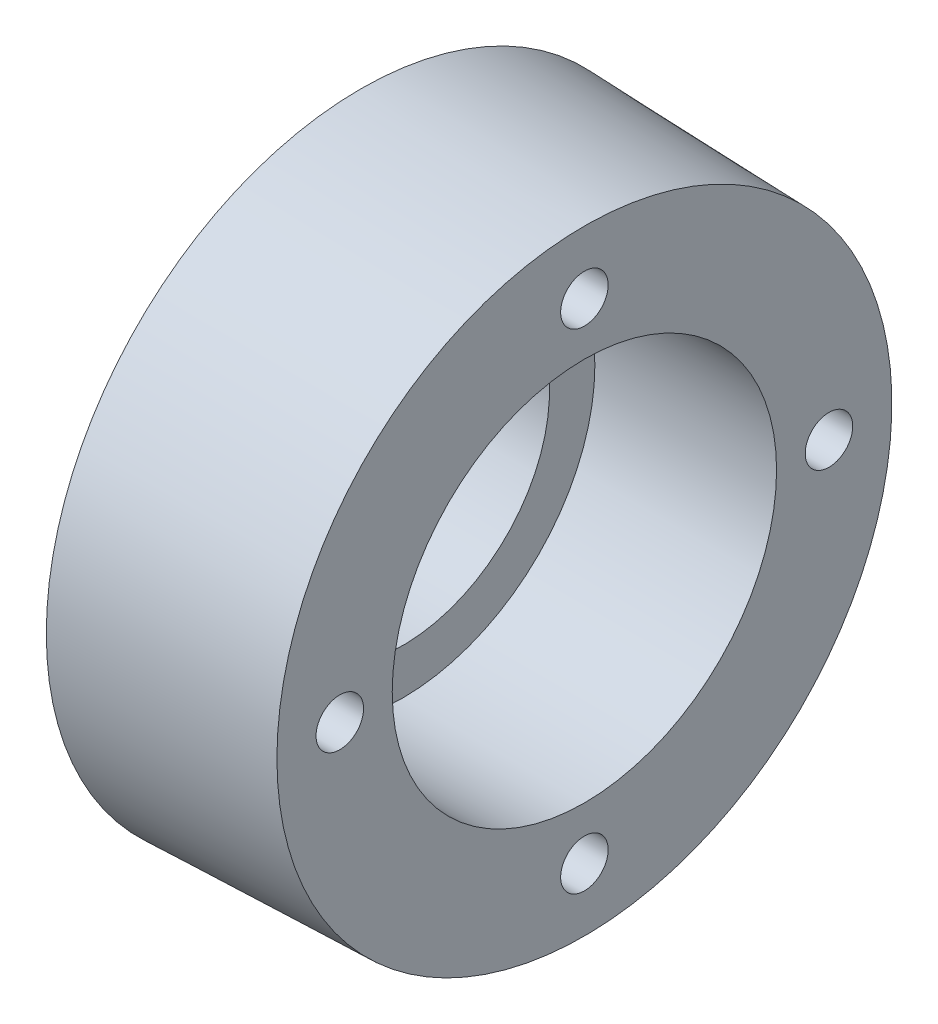
SolidWorks part; units mm, degrees
ref_plane "Front Plane" through (0, 0, 0) normal (0, 0, 1) x (1, 0, 0)
ref_plane "Top Plane" through (0, 0, 0) normal (0, 1, 0) x (1, 0, 0)
ref_plane "Right Plane" through (0, 0, 0) normal (1, 0, 0) x (0, 0, -1)
sketch "Çizim1" plane through (0, 0, 0) normal (0, 0, 1) x (1, 0, 0)
  line L0 (0, 0) -> (76.8972, 0) construction
  line L1 (0, 21) -> (11, 21)
  line L2 (0, 21) -> (0, 28)
  line L3 (0, 28) -> (5, 28)
  line L4 (5, 28) -> (5, 45)
  line L5 (5, 45) -> (37, 44)
  line L6 (37, 44) -> (37, 27.5)
  line L7 (37, 27.5) -> (11, 27.5)
  line L8 (11, 27.5) -> (11, 21) construction
  line L9 (11, 21) -> (11, 27.5) construction
  line L10 (11, 21) -> (11, 27.5)
  dimension "D1" = 21
  dimension "D2" = 28
  dimension "D3" = 27.5
  dimension "D4" = 5
  dimension "D5" = 45
  dimension "D6" = 88
  dimension "D7" = 37
  dimension "D8" = 26
revolve "Döndür1" add sketch "Çizim1" angle 360 about L0
hole_wizard "M8 Dişli Delik1" positions "Çizim2" profile "Çizim4" tap size "M8" standard "ISO"
sketch "Çizim2" plane through (37, 0, 0) normal (1, 0, 0) x (0, 0, -1)
  point P0 (0, 35)
  dimension "D1" = 35
sketch "Çizim4" plane through (37, 35, 0) normal (0, 1, 0) x (0, 0, -1)
  line L0 (0, 0) -> (0, 24.2929)
  line L1 (0, 24.2929) -> (3.4, 22.25)
  line L2 (3.4, 22.25) -> (3.4, 0)
  line L5 (3.4, 0) -> (0, 0)
  line L10 (0, 24.2929) -> (-3.4, 22.25) construction
  line L11 (0, -6.35) -> (0, 107.95) construction
  dimension "Tap Drill Dia." = 6.8
  dimension "Tap Drill Depth" = 22.25
  dimension "Drill Angle" = 118
cosmetic thread "Delik Dişi1"
pattern_circular "Dairesel Kaplama2" count 4 over 360 about axis through (0, 0, 0) along (1, 0, 0) of "M8 Dişli Delik1"
cosmetic thread "Delik Dişi2"
cosmetic thread "Delik Dişi3"
cosmetic thread "Delik Dişi4"
